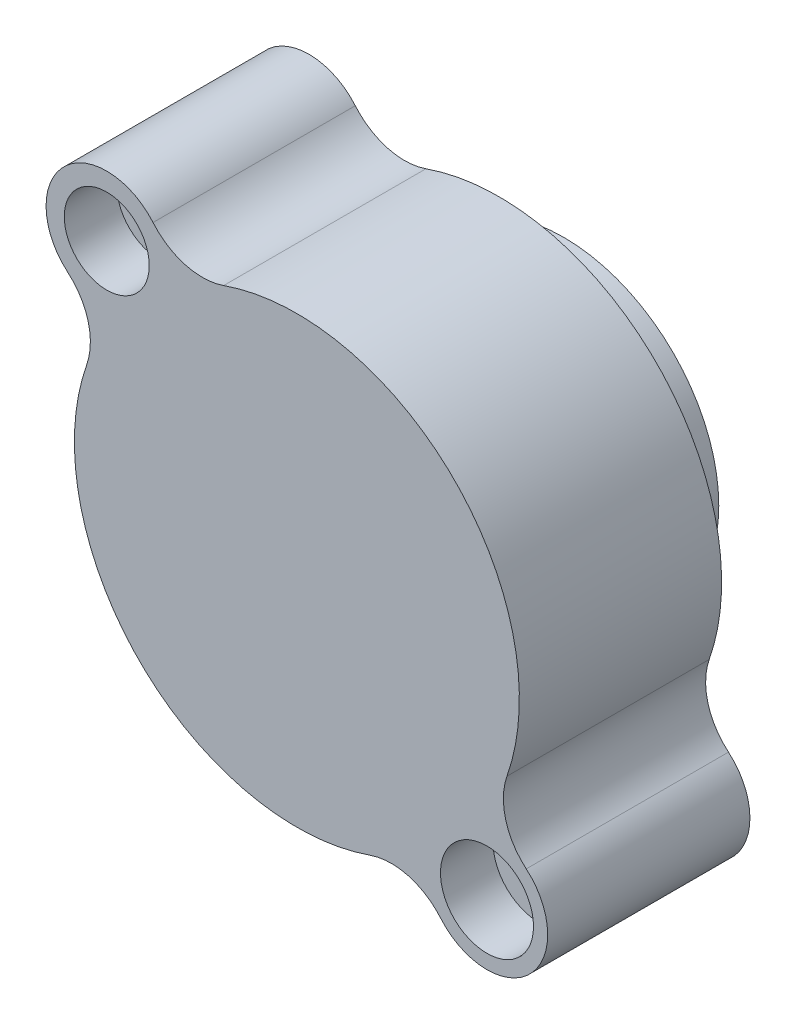
SolidWorks part; units mm, degrees
ref_plane "FRONT" through (0, 0, 0) normal (0, 0, 1) x (1, 0, 0)
ref_plane "TOP" through (0, 0, 0) normal (0, 1, 0) x (1, 0, 0)
ref_plane "RIGHT" through (0, 0, 0) normal (1, 0, 0) x (0, 0, -1)
ref_plane "Plan1" through (0, 0, 838.2) normal (0, 0, 1) x (1, 0, 0)
sketch "Esquisse1" plane through (0, 0, 838.2) normal (0, 0, 1) x (1, 0, 0)
  arc A0 (-720.1018, 451.6018) -> (-659.6259, 229.7738) centre (-851.517, 296.617) cw
  arc A1 (-659.6259, 229.7738) -> (229.7738, -659.6259) centre (0, 0) ccw
  arc A2 (229.7738, -659.6259) -> (451.6018, -720.1018) centre (296.617, -851.517) cw
  arc A3 (451.6018, -720.1018) -> (720.1018, -451.6018) centre (596.9, -596.9) ccw
  arc A4 (720.1018, -451.6018) -> (659.6259, -229.7738) centre (851.517, -296.617) cw
  arc A5 (659.6259, -229.7738) -> (-229.7738, 659.6259) centre (0, 0) ccw
  arc A6 (-229.7738, 659.6259) -> (-451.6018, 720.1018) centre (-296.617, 851.517) cw
  arc A7 (-451.6018, 720.1018) -> (-720.1018, 451.6018) centre (-596.9, 596.9) ccw
extrude "Boss.-Extru.1" add sketch "Esquisse1" against normal blind 635
sketch "Esquisse2" plane through (0, 0, 203.2) normal (0, 0, -1) x (-1, 0, 0)
  circle A0 centre (0, 0) radius 486.41
  dimension "D1" = 972.82
extrude "Boss.-Extru.2" add sketch "Esquisse2" along normal blind 203.2
sketch "Esquisse3" plane through (0, 0, 838.2) normal (0, 0, 1) x (1, 0, 0)
  circle A0 centre (0, 0) radius 20
  dimension "D1" = 40
hole_wizard "Perçage1" positions "Esquisse6" profile "Esquisse5" legacy
sketch "Esquisse6" plane through (0, 0, 838.2) normal (0, 0, 1) x (1, 0, 0)
  point P0 (-596.9, 596.9)
sketch "Esquisse5" plane through (-596.9, 596.9, 838.2) normal (1, 0, 0) x (0, -1, 0)
  line L0 (0, 0) -> (0, 838.2)
  line L1 (0, 838.2) -> (69.85, 838.2)
  line L2 (69.85, 838.2) -> (69.85, 165.1)
  line L3 (69.85, 165.1) -> (133.35, 165.1)
  line L4 (133.35, 165.1) -> (133.35, 0)
  line L5 (133.35, 0) -> (0, 0)
  line L6 (0, 110) -> (0, -10) construction
  dimension "Diamètre" = 139.7
  dimension "Profondeur" = 838.2
  dimension "Diamètre chambrage" = 266.7
  dimension "Profondeur chambrage" = 165.1
hole_wizard "Perçage2" positions "Esquisse8" profile "Esquisse7" legacy
sketch "Esquisse8" plane through (0, 0, 838.2) normal (0, 0, 1) x (1, 0, 0)
  point P0 (596.9, -596.9)
sketch "Esquisse7" plane through (596.9, -596.9, 838.2) normal (1, 0, 0) x (0, -1, 0)
  line L0 (0, 0) -> (0, 838.2)
  line L1 (0, 838.2) -> (69.85, 838.2)
  line L2 (69.85, 838.2) -> (69.85, 165.1)
  line L3 (69.85, 165.1) -> (146.05, 165.1)
  line L4 (146.05, 165.1) -> (146.05, 0)
  line L5 (146.05, 0) -> (0, 0)
  line L6 (0, 110) -> (0, -10) construction
  dimension "Diamètre" = 139.7
  dimension "Profondeur" = 838.2
  dimension "Diamètre chambrage" = 292.1
  dimension "Profondeur chambrage" = 165.1
